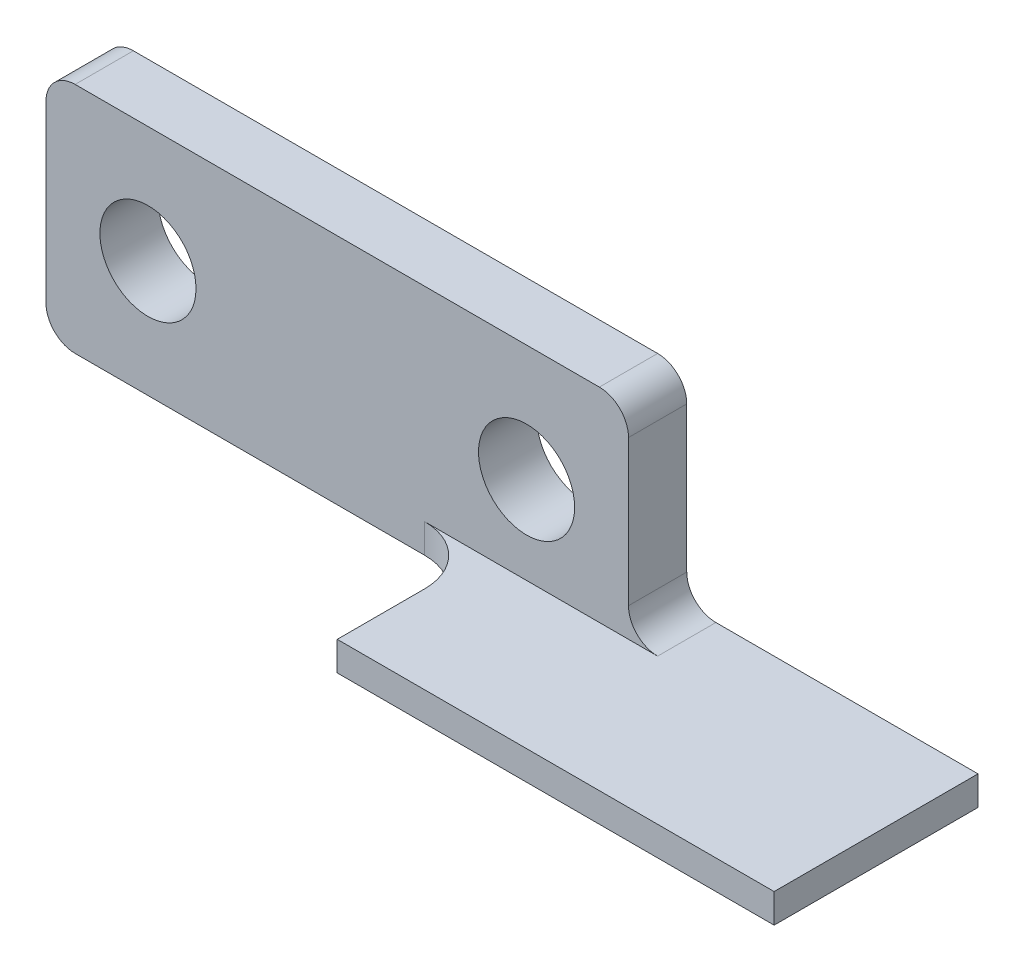
SolidWorks part; units mm, degrees
ref_plane "Front Plane" through (0, 0, 0) normal (0, 0, 1) x (1, 0, 0)
ref_plane "Top Plane" through (0, 0, 0) normal (0, 1, 0) x (1, 0, 0)
ref_plane "Right Plane" through (0, 0, 0) normal (1, 0, 0) x (0, 0, -1)
sketch "Sketch1" plane through (0, 0, 0) normal (0, 0, 1) x (1, 0, 0)
  line L1 (0, 0) -> (20, 0)
  line L2 (0, 0) -> (0, 8)
  line L3 (0, 8) -> (20, 8)
  line L4 (20, 0) -> (20, 8)
  dimension "D1" = 8
  dimension "D2" = 20
extrude "Boss-Extrude1" add sketch "Sketch1" along normal blind 2
sketch "Sketch2" plane through (0, 0, 2) normal (0, 0, 1) x (1, 0, 0)
  line L0 (0, 0) -> (20, 0) construction
  line L1 (15, 0) -> (30, 0)
  line L2 (15, 0) -> (15, 1)
  line L3 (15, 1) -> (30, 1)
  line L4 (30, 0) -> (30, 1)
  line L5 (20, 0) -> (20, 8) construction
  dimension "D1" = 1
  dimension "D2" = 5
  dimension "D3" = 10
extrude "Boss-Extrude2" add sketch "Sketch2" along normal blind 5 and the other way blind 2
sketch "Sketch3" plane through (0, 0, 2) normal (0, 0, 1) x (1, 0, 0)
  line L0 (0, 4) -> (21.323, 4) construction
  line L1 (0, 8) -> (0, 0) construction
  circle A0 centre (3.5, 4) radius 1.65
  circle A1 centre (16.5, 4) radius 1.65
  dimension "D1" = 3.3
  dimension "D2" = 3.5
  dimension "D3" = 13
extrude "Cut-Extrude1" cut sketch "Sketch3" against normal through all
fillet "Fillet1" radius 1 4 edges at (20, 8, 1) (0, 8, 1) (0, 0, 1) (20, 1, 1)
fillet "Fillet2" radius 2 1 edges at (15, 0.5, 2)
